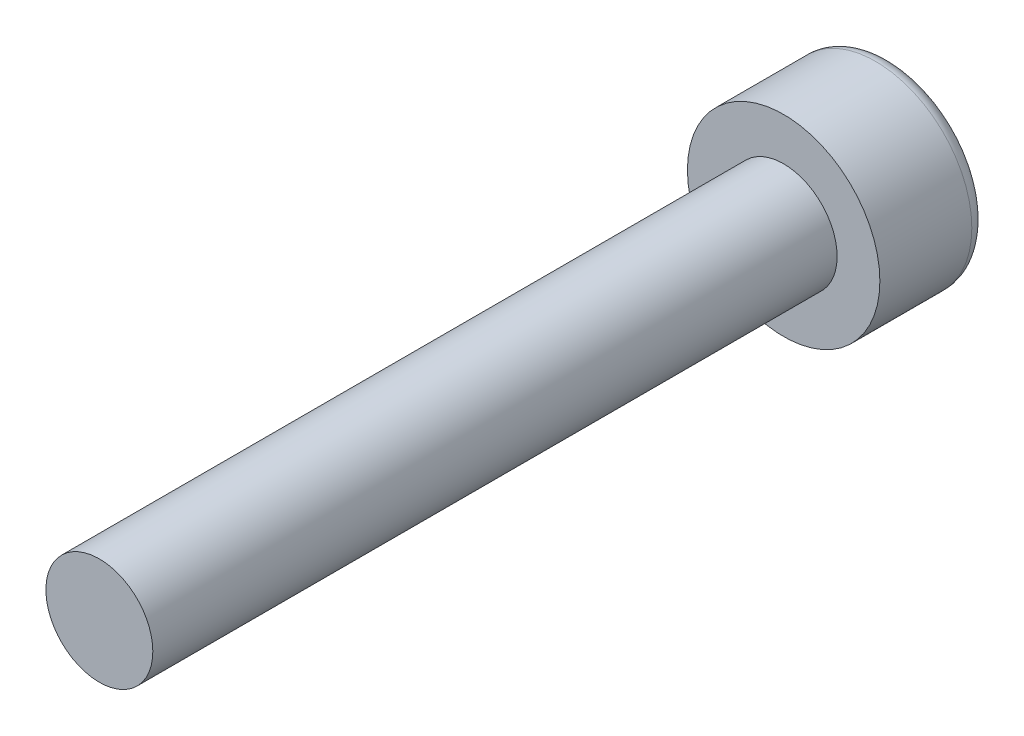
SolidWorks part; units mm, degrees
material "Acero aleado"
ref_plane "Alzado" through (0, 0, 0) normal (0, 0, 1) x (1, 0, 0)
ref_plane "Planta" through (0, 0, 0) normal (0, 1, 0) x (1, 0, 0)
ref_plane "Vista lateral" through (0, 0, 0) normal (1, 0, 0) x (0, 0, -1)
sketch "Croquis1" plane through (0, 0, 0) normal (0, 0, 1) x (1, 0, 0)
  circle A0 centre (0, 0) radius 1.25
  dimension "D1" = 2.5
extrude "Saliente-Extruir1" add sketch "Croquis1" along normal blind 16
sketch "Croquis2" plane through (0, 0, 0) normal (0, 0, -1) x (-1, 0, 0)
  circle A0 centre (0, 0) radius 2.25
  dimension "D1" = 4.5
extrude "Saliente-Extruir2" add sketch "Croquis2" along normal blind 2.5
sketch "Croquis3" plane through (0, 0, -2.5) normal (0, 0, -1) x (-1, 0, 0)
  line L1 (0, -1.1547) -> (1, -0.5774)
  line L2 (1, -0.5774) -> (1, 0.5774)
  line L3 (1, 0.5774) -> (0, 1.1547)
  line L4 (0, 1.1547) -> (-1, 0.5774)
  line L5 (-1, 0.5774) -> (-1, -0.5774)
  line L6 (-1, -0.5774) -> (0, -1.1547)
  circle A0 centre (0, 0) radius 1 construction
  dimension "D1" = 2
extrude "Cortar-Extruir1" cut sketch "Croquis3" against normal blind 1.5
fillet "Redondeo1" radius 0.35 1 edges at (-2.25, 0, -2.5)
